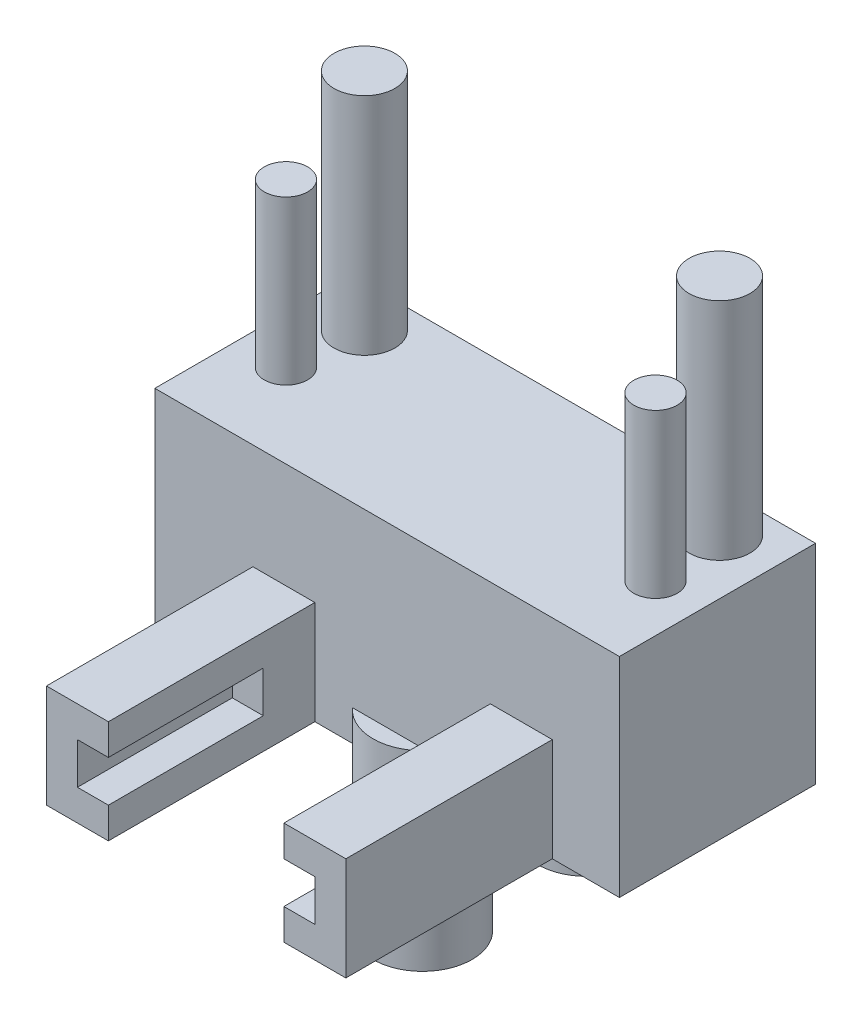
SolidWorks part; units mm, degrees
ref_plane "Front Plane" through (0, 0, 0) normal (0, 0, 1) x (1, 0, 0)
ref_plane "Top Plane" through (0, 0, 0) normal (0, 1, 0) x (1, 0, 0)
ref_plane "Right Plane" through (0, 0, 0) normal (1, 0, 0) x (0, 0, -1)
sketch "Sketch1" plane through (0, 0, 0) normal (0, 1, 0) x (1, 0, 0)
  line L1 (-40.1858, -24.5795) -> (-17.6858, -24.5795)
  line L2 (-40.1858, -24.5795) -> (-40.1858, -17.5795)
  line L3 (-40.1858, -17.5795) -> (-17.6858, -17.5795)
  line L4 (-17.6858, -24.5795) -> (-17.6858, -17.5795)
  dimension "D1" = 22.5
  dimension "D2" = 7
extrude "Boss-Extrude1" add sketch "Sketch1" along normal blind 1.5
sketch "Sketch2" plane through (0, 1.5, 0) normal (0, 1, 0) x (1, 0, 0)
  line L0 (-17.6858, -24.5795) -> (-17.6858, -17.5795) construction
  line L2 (-40.1858, -24.5795) -> (-17.6858, -24.5795) construction
  circle A0 centre (-37.5358, -19.5795) radius 1.475
  circle A1 centre (-20.3358, -19.5795) radius 1.475
  dimension "D1" = 2.95
  dimension "D2" = 2.95
  dimension "D3" = 17.2
  dimension "D4" = 2.65
  dimension "D5" = 5
  dimension "D6" = 5
extrude "Boss-Extrude2" add sketch "Sketch2" along normal blind 13.5
sketch "Sketch3" plane through (0, 1.5, 0) normal (0, 1, 0) x (1, 0, 0)
  circle A0 centre (-37.8858, -23.0295) radius 1.05
  circle A1 centre (-19.9858, -23.0295) radius 1.05
  circle A2 centre (-37.5358, -19.5795) radius 1.475 construction
  circle A3 centre (-20.3358, -19.5795) radius 1.475 construction
  dimension "D1" = 2.1
  dimension "D2" = 2.1
  dimension "D3" = 0.35
  dimension "D4" = 0.35
  dimension "D5" = 3.45
  dimension "D6" = 3.45
extrude "Boss-Extrude3" add sketch "Sketch3" along normal blind 10.5
sketch "Sketch4" plane through (0, 0, 0) normal (0, -1, 0) x (-1, 0, 0)
  line L0 (40.1858, -17.5795) -> (40.1858, -24.5795) construction
  line L1 (17.6858, -24.5795) -> (40.1858, -24.5795)
  line L2 (17.6858, -24.5795) -> (17.6858, -27.0795)
  line L3 (17.6858, -27.0795) -> (40.1858, -27.0795)
  line L4 (40.1858, -24.5795) -> (40.1858, -27.0795)
  line L6 (20.9358, -27.0795) -> (23.9358, -27.0795)
  line L7 (20.9358, -27.0795) -> (20.9358, -29.9823)
  line L8 (20.9358, -29.9823) -> (23.9358, -29.9823)
  line L9 (23.9358, -27.0795) -> (23.9358, -29.9823)
  line L10 (32.4358, -27.0795) -> (35.4358, -27.0795)
  line L11 (32.4358, -27.0795) -> (32.4358, -28.8632)
  line L12 (32.4358, -28.8632) -> (35.4358, -28.8632)
  line L13 (35.4358, -27.0795) -> (35.4358, -28.8632)
  line M13 (40.1858, -24.5795) -> (40.1858, -17.5795)
  line M14 (40.1858, -17.5795) -> (17.6858, -17.5795)
  line M15 (17.6858, -17.5795) -> (17.6858, -24.5795)
  line M16 (17.6858, -24.5795) -> (40.1858, -24.5795)
  dimension "D1" = 0
  dimension "D2" = 3.25
  dimension "D3" = 4.75
  dimension "D4" = 2.5
  dimension "D5" = 3
  dimension "D6" = 3
extrude "Boss-Extrude4" add sketch "Sketch4" along normal blind 6 and the other way blind 1.5 contours L4 L2 L3 M16 | M16 M13 M14 M15
sketch "Sketch5" plane through (0, -6, 0) normal (0, -1, 0) x (-1, 0, 0)
  line L0 (17.6858, -27.0795) -> (40.1858, -27.0795) construction
  line L1 (35.4358, -27.0795) -> (32.4358, -27.0795)
  line L2 (35.4358, -27.0795) -> (35.4358, -37.0795)
  line L3 (35.4358, -37.0795) -> (32.4358, -37.0795)
  line L4 (32.4358, -27.0795) -> (32.4358, -37.0795)
  line L5 (17.6858, -17.5795) -> (17.6858, -27.0795) construction
  line L6 (23.9358, -27.0795) -> (20.9358, -27.0795)
  line L7 (23.9358, -27.0795) -> (23.9358, -37.0795)
  line L8 (23.9358, -37.0795) -> (20.9358, -37.0795)
  line L9 (20.9358, -27.0795) -> (20.9358, -37.0795)
  line L10 (40.1858, -17.5795) -> (40.1858, -27.0795) construction
  dimension "D1" = 3.25
  dimension "D2" = 4.75
  dimension "D3" = 3
  dimension "D4" = 3
  dimension "D5" = 10
  dimension "D6" = 10
extrude "Boss-Extrude6" add sketch "Sketch5" against normal blind 5
sketch "Sketch7" plane through (0, 0, 37.0795) normal (0, 0, 1) x (1, 0, 0)
  line L0 (-35.4358, -1) -> (-35.4358, -6) construction
  line L1 (-22.4358, -4.5) -> (-33.9358, -4.5)
  line L2 (-22.4358, -4.5) -> (-22.4358, -2.5)
  line L3 (-22.4358, -2.5) -> (-33.9358, -2.5)
  line L4 (-33.9358, -4.5) -> (-33.9358, -2.5)
  line L5 (-32.4358, -1) -> (-35.4358, -1) construction
  line L6 (-32.4358, -6) -> (-35.4358, -6) construction
  line L7 (-20.9358, -1) -> (-20.9358, -6) construction
  dimension "D1" = 1.5
  dimension "D2" = 1.5
  dimension "D3" = 1.5
  dimension "D4" = 1.5
extrude "Cut-Extrude1" cut sketch "Sketch7" against normal blind 7.5
sketch "Sketch8" plane through (0, 1.5, 0) normal (0, 1, 0) x (1, 0, 0)
  line L1 (-40.1858, -17.5795) -> (-17.6858, -17.5795)
  line L2 (-40.1858, -17.5795) -> (-40.1858, -27.0795)
  line L3 (-40.1858, -27.0795) -> (-17.6858, -27.0795)
  line L4 (-17.6858, -17.5795) -> (-17.6858, -27.0795)
extrude "Boss-Extrude7" add sketch "Sketch8" along normal blind 2.61
sketch "Sketch9" plane through (0, -6, 0) normal (0, -1, 0) x (-1, 0, 0)
  line L0 (17.6858, -17.5795) -> (17.6858, -27.0795) construction
  line L3 (23.9358, -27.0795) -> (32.4358, -27.0795) construction
  circle A0 centre (28.8108, -25.4895) radius 2.4
  circle A1 centre (28.8108, -17.5195) radius 2.4
  dimension "D1" = 11.125
  dimension "D2" = 11.125
  dimension "D3" = 4.8
  dimension "D4" = 4.8
  dimension "D5" = 1.59
  dimension "D6" = 7.97
extrude "Boss-Extrude8" add sketch "Sketch9" along normal blind 7.76 and the other way blind 1.5
sketch "Sketch10" plane through (0, -6, 0) normal (0, -1, 0) x (-1, 0, 0)
  line L1 (40.1858, -27.0795) -> (17.6858, -27.0795)
  line L2 (40.1858, -27.0795) -> (40.1858, -17.5795)
  line L3 (40.1858, -17.5795) -> (17.6858, -17.5795)
  line L4 (17.6858, -27.0795) -> (17.6858, -17.5795)
